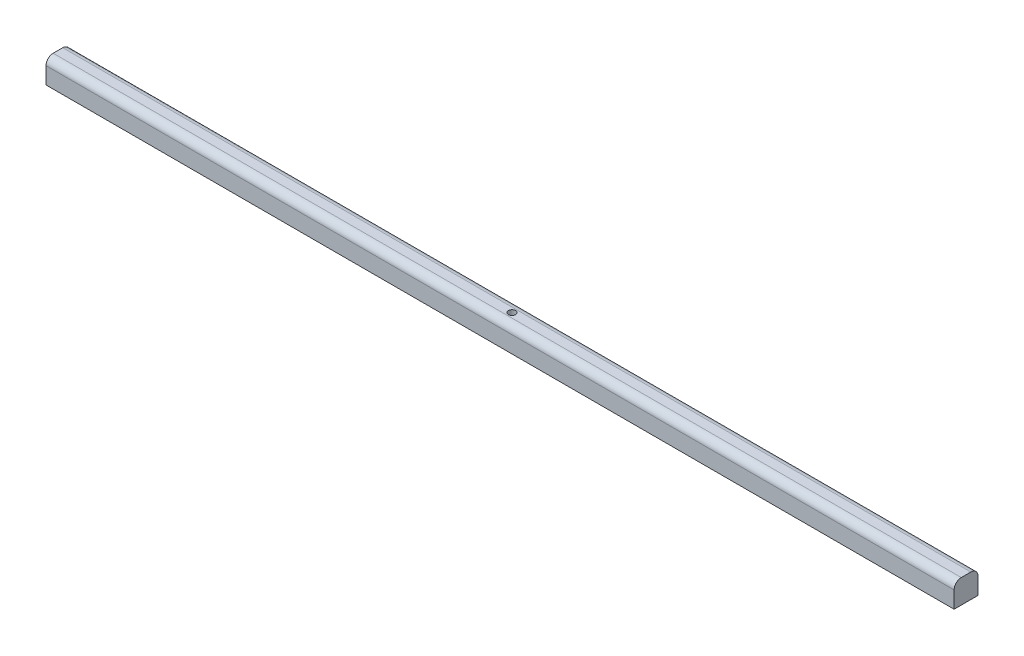
SolidWorks part; units mm, degrees
ref_plane "Front Plane" through (0, 0, 0) normal (0, 0, 1) x (1, 0, 0)
ref_plane "Top Plane" through (0, 0, 0) normal (0, 1, 0) x (1, 0, 0)
ref_plane "Right Plane" through (0, 0, 0) normal (1, 0, 0) x (0, 0, -1)
sketch "Sketch1" plane through (0, 0, 0) normal (0, 1, 0) x (1, 0, 0)
  line L1 (-190, 5) -> (190, 5)
  line L2 (-190, 5) -> (-190, -5)
  line L3 (-190, -5) -> (190, -5)
  line L4 (190, 5) -> (190, -5)
  line L5 (-190, 5) -> (190, -5) construction
  line L6 (-190, -5) -> (190, 5) construction
  point P0 (0, 0)
extrude "Boss-Extrude1" add sketch "Sketch1" along normal blind 10
fillet "Fillet1" radius 3 2 edges at (0, 10, -5) (0, 10, 5)
sketch "Sketch2" plane through (0, 0, 0) normal (0, -1, 0) x (1, 0, 0)
  circle A0 centre (0, 0) radius 1.5
extrude "Cut-Extrude1" cut sketch "Sketch2" against normal blind 10
